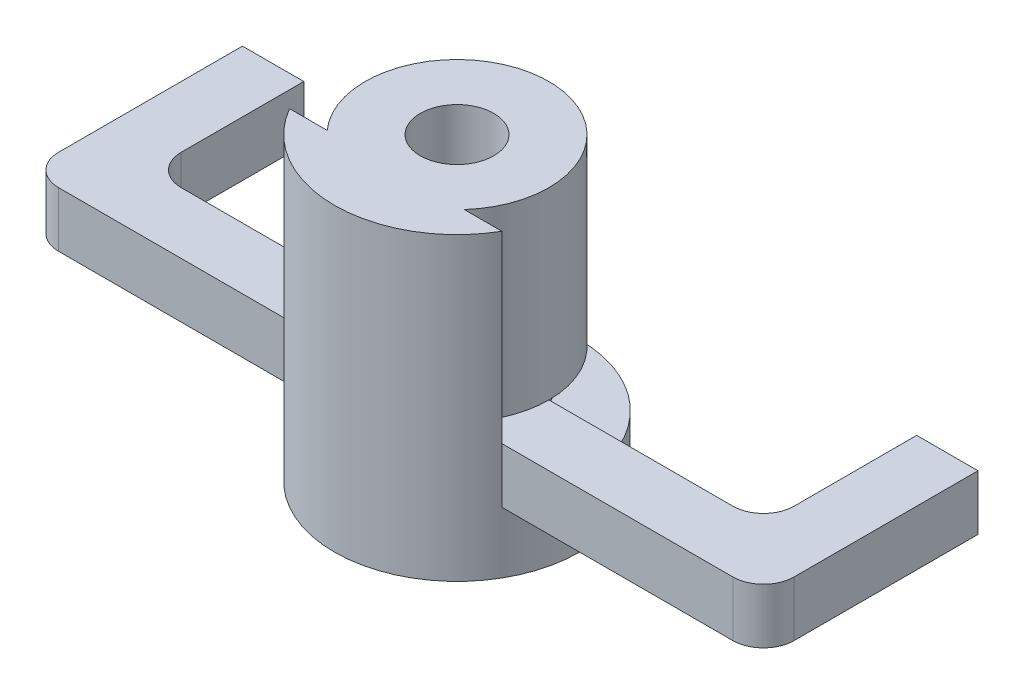
SolidWorks part; units mm, degrees
ref_plane "Plan de face" through (0, 0, 0) normal (0, 0, 1) x (1, 0, 0)
ref_plane "Plan de dessus" through (0, 0, 0) normal (0, 1, 0) x (1, 0, 0)
ref_plane "Plan de droite" through (0, 0, 0) normal (1, 0, 0) x (0, 0, -1)
sketch "Esquisse1" plane through (0, 0, 0) normal (0, 1, 0) x (1, 0, 0)
  line L0 (-10, 0) -> (-12, 0)
  line L2 (-10, 0) -> (-10, -5)
  line L4 (10, 0) -> (10, -5)
  line L5 (-12, 0) -> (-12, -7)
  line L7 (12, -7) -> (12, 0)
  line L8 (12, 0) -> (10, 0)
  line L9 (-2, -5) -> (-10, -5)
  line L10 (2, -5) -> (10, -5)
  line L11 (-12, -7) -> (-3.4641, -7)
  line L12 (3.4641, -7) -> (12, -7)
  arc A0 (-2, -5) -> (2, -5) centre (0, -5) ccw
  arc A1 (-3.4641, -7) -> (3.4641, -7) centre (0, -5) ccw
  dimension "D6" = 2
  dimension "D8" = 4
  dimension "D1" = 20
  dimension "D2" = 10
  dimension "D3" = 5
  dimension "D4" = 2
  dimension "D5" = 2
  dimension "D7" = 2
extrude "Boss.-Extru.1" add sketch "Esquisse1" along normal blind 1.8
fillet "Congé1" radius 1 4 edges at (-12, 0.9, 7) (12, 0.9, 7) (10, 0.9, 5) (-10, 0.9, 5)
sketch "Esquisse4" plane through (0, 0, 0) normal (0, -1, 0) x (1, 0, 0)
  circle A0 centre (0, 5) radius 4
  arc A1 (3.4641, 7) -> (-3.4641, 7) centre (0, 5) ccw construction
extrude "Boss.-Extru.3" add sketch "Esquisse4" along normal blind 2
sketch "Esquisse5" plane through (0, -2, 0) normal (0, -1, 0) x (1, 0, 0)
  line L0 (3.4641, 7) -> (11, 7) construction
  line L1 (-1.15, 6.9919) -> (-2.3, 5)
  line L2 (-2.3, 5) -> (-1.15, 3.0081)
  line L3 (-1.15, 3.0081) -> (1.15, 3.0081)
  line L4 (1.15, 3.0081) -> (2.3, 5)
  line L5 (2.3, 5) -> (1.15, 6.9919)
  line L6 (1.15, 6.9919) -> (-1.15, 6.9919)
  circle A0 centre (0, 5) radius 1.9919 construction
  circle A1 centre (0, 5) radius 4 construction
  dimension "D1" = 2.3
extrude "Enlèv. mat.-Extru.1" cut sketch "Esquisse5" against normal blind 11
sketch "Esquisse6" plane through (0, 1.8, 0) normal (0, 1, 0) x (1, 0, 0)
  circle A0 centre (0, -5) radius 3
  arc A1 (-3.4641, -7) -> (3.4641, -7) centre (0, -5) ccw construction
  circle A2 centre (0, -5) radius 1.2
  dimension "D1" = 6
  dimension "D2" = 2.4
extrude "Boss.-Extru.4" add sketch "Esquisse6" along normal blind 6
sketch "Esquisse7" plane through (0, 1.8, 0) normal (0, 1, 0) x (1, 0, 0)
  line L0 (-3.4641, -7) -> (3.4641, -7)
  arc A0 (-3.4641, -7) -> (3.4641, -7) centre (0, -5) ccw construction
  arc A1 (-3.4641, -7) -> (3.4641, -7) centre (0, -5) ccw
extrude "Boss.-Extru.5" add sketch "Esquisse7" along normal up to surface (6 mm away) up to face at (0, 7.8, 8)
